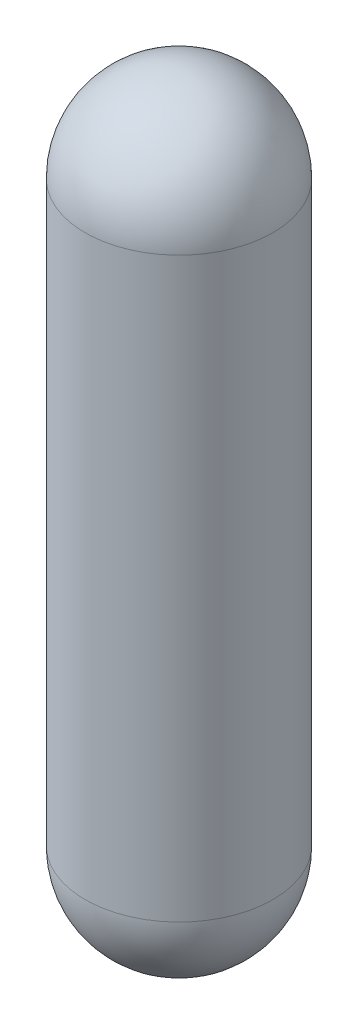
SolidWorks part; units mm, degrees
material "Titanium"
ref_plane "Front Plane" through (0, 0, 0) normal (0, 0, 1) x (1, 0, 0)
ref_plane "Top Plane" through (0, 0, 0) normal (0, 1, 0) x (1, 0, 0)
ref_plane "Right Plane" through (0, 0, 0) normal (1, 0, 0) x (0, 0, -1)
sketch "Sketch1" plane through (0, 0, 0) normal (0, 0, 1) x (1, 0, 0)
  line L0 (0, 1766.6705) -> (0, 2306.4205)
  line L1 (0, -1553.8295) -> (539.75, -1553.8295) construction
  line L2 (0, -1553.8295) -> (0, 1766.6705)
  line L3 (0, 1766.6705) -> (539.75, 1766.6705) construction
  line L4 (539.75, -1553.8295) -> (539.75, 1766.6705)
  line L5 (0, -1553.8295) -> (0, -2093.5795)
  arc A0 (539.75, 1766.6705) -> (0, 2306.4205) centre (0, 1766.6705) ccw
  arc A1 (539.75, -1553.8295) -> (0, -2093.5795) centre (0, -1553.8295) cw
  dimension "D3" = 539.75
  dimension "D4" = 539.75
  dimension "D1" = 4400
  dimension "D2" = 539.75
revolve "Revolve1" add sketch "Sketch1" angle 360 about L2
